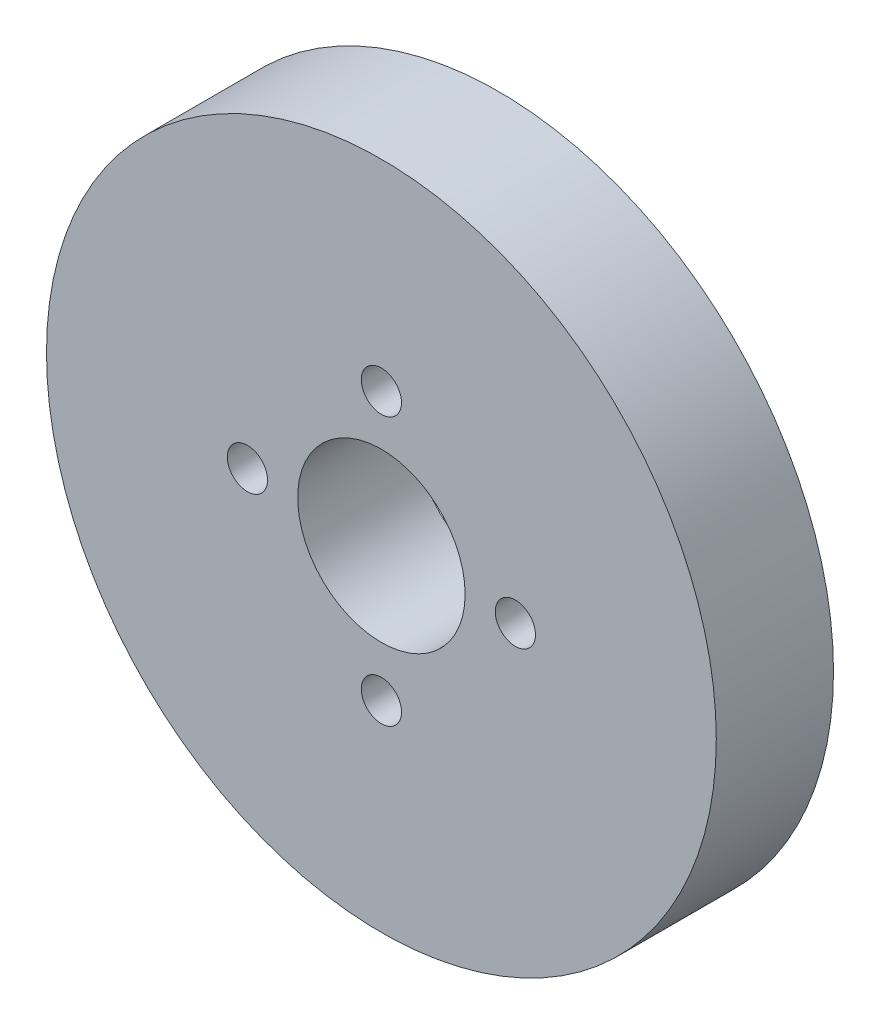
SolidWorks part; units mm, degrees
ref_plane "Plan de face" through (0, 0, 0) normal (0, 0, 1) x (1, 0, 0)
ref_plane "Plan de dessus" through (0, 0, 0) normal (0, 1, 0) x (1, 0, 0)
ref_plane "Plan de droite" through (0, 0, 0) normal (1, 0, 0) x (0, 0, -1)
sketch "Esquisse1" plane through (0, 0, 0) normal (0, 0, 1) x (1, 0, 0)
  circle A0 centre (0, 0) radius 20
  circle A1 centre (0, 0) radius 5
  dimension "D1" = 10
  dimension "D2" = 40
extrude "Boss.-Extru.1" add sketch "Esquisse1" along normal blind 7
hole_wizard "Dégagement M21" positions "Esquisse4" profile "Esquisse3" size "M2" standard "ISO" slot yes end condition through all
sketch "Esquisse4" plane through (0, 0, 7) normal (0, 0, 1) x (1, 0, 0)
  point P0 (0, 8)
  point P7 (8, 0)
  point P8 (0, -8)
  point P9 (-8, 0)
  point P10 (0, 0)
  dimension "D1" = 8
  dimension "D2" = 4
sketch "Esquisse3" plane through (0, 8, 7) normal (1, 0, 0) x (0, -1, 0)
  line L0 (0, 0) -> (0, 7)
  line L1 (0, 7) -> (1.2, 7)
  line L2 (1.2, 7) -> (1.2, 0)
  line L5 (1.2, 0) -> (0, 0)
  line L11 (0, -6.35) -> (0, 107.95) construction
  dimension "Diamètre du perçage jusqu'au prochain" = 2.4
  dimension "Profondeur du perçage jusqu'au prochain" = 7
